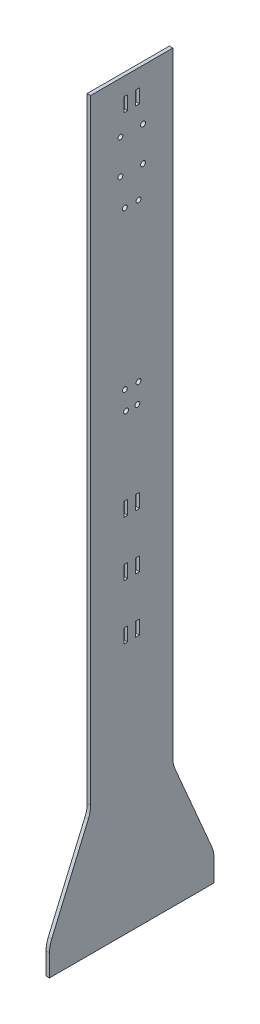
SolidWorks part; units mm, degrees
ref_plane "Front Plane" through (0, 0, 0) normal (0, 0, 1) x (1, 0, 0)
ref_plane "Top Plane" through (0, 0, 0) normal (0, 1, 0) x (1, 0, 0)
ref_plane "Right Plane" through (0, 0, 0) normal (1, 0, 0) x (0, 0, -1)
sketch "Sketch1" plane through (0, 0, 0) normal (1, 0, 0) x (0, 0, -1)
  line L1 (-38.1, 457.2) -> (38.1, 457.2)
  line L2 (-38.1, 457.2) -> (-38.1, -457.2)
  line L3 (-38.1, -457.2) -> (38.1, -457.2)
  line L4 (38.1, 457.2) -> (38.1, -457.2)
  line L5 (-38.1, 457.2) -> (38.1, -457.2) construction
  line L6 (-38.1, -457.2) -> (38.1, 457.2) construction
  point P0 (0, 0)
  dimension "D1" = 914.4
  dimension "D2" = 76.2
extrude "Boss-Extrude1" add sketch "Sketch1" along normal blind 3.175
sketch "Sketch2" plane through (3.175, 0, 0) normal (1, 0, 0) x (0, 0, -1)
  line L0 (-38.1, -457.2) -> (38.1, -457.2) construction
  line L1 (3.722, -204.5335) -> (7.278, -204.5335)
  line L2 (3.722, -204.5335) -> (3.722, -217.4875)
  line L3 (3.722, -217.4875) -> (7.278, -217.4875)
  line L4 (7.278, -204.5335) -> (7.278, -217.4875)
  line L5 (3.722, -204.5335) -> (7.278, -217.4875) construction
  line L6 (3.722, -217.4875) -> (7.278, -204.5335) construction
  point P0 (5.5, -211.0105)
  dimension "D1" = 3.556
  dimension "D2" = 12.954
  dimension "D3" = 239.7125
  dimension "D4" = 3.722
extrude "Cut-Extrude1" cut sketch "Sketch2" against normal through all
mirror "Mirror1" about plane through (0, 0, 0) normal (0, 0, 1) of "Cut-Extrude1"
pattern_linear "LPattern1" count 2 spacing 50.8 along (0, 1, 0) count 2 spacing 50.8 along (0, -1, 0) of "Mirror1", "Cut-Extrude1"
sketch "Sketch3" plane through (3.175, 0, 0) normal (1, 0, 0) x (0, 0, -1)
  line L0 (7.278, -153.7335) -> (3.722, -153.7335) construction
  line L1 (3.722, 170.9081) -> (7.278, 170.9081)
  line L2 (3.722, 170.9081) -> (3.722, 157.9541)
  line L3 (3.722, 157.9541) -> (7.278, 157.9541)
  line L4 (7.278, 170.9081) -> (7.278, 157.9541)
  line L5 (3.722, 170.9081) -> (7.278, 157.9541) construction
  line L6 (3.722, 157.9541) -> (7.278, 170.9081) construction
  line L7 (7.278, -166.6875) -> (7.278, -153.7335) construction
  line L9 (0, 0) -> (0, 53.0447) construction
  line L10 (-3.722, 157.9541) -> (-7.278, 170.9081) construction
  line L11 (-3.722, 170.9081) -> (-7.278, 157.9541) construction
  line L12 (-7.278, 170.9081) -> (-7.278, 157.9541)
  line L13 (-3.722, 157.9541) -> (-7.278, 157.9541)
  line L14 (-3.722, 170.9081) -> (-3.722, 157.9541)
  line L15 (-3.722, 170.9081) -> (-7.278, 170.9081)
  point P0 (5.5, 164.4311)
  point P19 (-5.5, 164.4311)
extrude "Cut-Extrude2" cut sketch "Sketch3" against normal through all
hole_wizard "#8 Clearance Hole1" positions "Sketch4" profile "Sketch5" hole size "#8" standard "ANSI Inch" end condition through all
sketch "Sketch4" plane through (3.175, 0, 0) normal (1, 0, 0) x (0, 0, -1)
  point P0 (6.35, -64.5237)
  point P3 (-6.35, -64.5237)
  point P6 (6.35, 81.272)
  point P9 (-6.35, 81.272)
  point P12 (5.25, -82.2261)
  point P15 (-5.25, -82.2261)
sketch "Sketch5" plane through (3.175, -64.5237, -6.35) normal (0, 1, 0) x (0, 0, -1)
  line L0 (0, 0) -> (0, 3.175)
  line L1 (0, 3.175) -> (2.2479, 3.175)
  line L2 (2.2479, 3.175) -> (2.2479, 0)
  line L5 (2.2479, 0) -> (0, 0)
  line L11 (0, -6.35) -> (0, 107.95) construction
  dimension "Thru Hole Dia." = 4.4958
  dimension "Thru Hole Depth" = 3.175
sketch "Sketch6" plane through (3.175, 0, 0) normal (1, 0, 0) x (0, 0, -1)
  line L0 (0, -457.2) -> (0, 187.325) construction
  line L1 (-38.1, -457.2) -> (38.1, -457.2) construction
  line L2 (-38.1, 187.325) -> (38.1, 187.325)
  line L4 (-38.1, 457.2) -> (-38.1, -457.2) construction
  line L5 (38.1, -457.2) -> (38.1, 457.2) construction
  dimension "D1" = 644.525
extrude "Cut-Extrude3" cut sketch "Sketch6" against normal through all and the other way through all
sketch "Sketch7" plane through (3.175, 0, 0) normal (1, 0, 0) x (0, 0, -1)
  line L0 (0, -457.2) -> (0, -501.65) construction
  line L1 (-38.1, -457.2) -> (38.1, -457.2) construction
  line L2 (-38.1, -457.2) -> (-38.1, -501.65)
  line L3 (-38.1, -501.65) -> (0, -501.65)
  line L4 (38.1, -457.2) -> (38.1, -501.65)
  line L5 (38.1, -501.65) -> (0, -501.65)
  line L6 (-38.1, -457.2) -> (38.1, -457.2)
  dimension "D1" = 44.45
extrude "Boss-Extrude2" add sketch "Sketch7" against normal up to surface (3.175 mm away) up to face at (0, -160.2105, 5.5)
sketch "Sketch8" plane through (3.175, 0, 0) normal (1, 0, 0) x (0, 0, -1)
  line L0 (-38.1, -387.35) -> (-76.2, -476.25)
  line L1 (-38.1, 187.325) -> (-38.1, -501.65) construction
  line L2 (-76.2, -476.25) -> (-76.2, -501.65)
  line L3 (-76.2, -501.65) -> (76.2, -501.65)
  line L4 (76.2, -501.65) -> (76.2, -476.25)
  line L5 (76.2, -476.25) -> (38.1, -387.35)
  line L6 (38.1, -501.65) -> (38.1, 187.325) construction
  line L7 (-38.1, -501.65) -> (38.1, -501.65) construction
  line L8 (-38.1, -387.35) -> (38.1, -387.35)
  dimension "D1" = 152.4
  dimension "D2" = 38.1
  dimension "D3" = 25.4
  dimension "D4" = 114.3
extrude "Boss-Extrude3" add sketch "Sketch8" against normal blind 3.175
fillet "Fillet1" radius 25.4 4 edges at (1.5875, -476.25, -76.2) (1.5875, -476.25, 76.2) (1.5875, -387.35, 38.1) (1.5875, -387.35, -38.1)
hole_wizard "#8 Clearance Hole2" positions "Sketch9" profile "Sketch10" hole size "#8" standard "ANSI Inch" end condition through all
sketch "Sketch9" plane through (0, 0, 0) normal (-1, 0, 0) x (0, 0, 1)
  point P0 (10.4775, 108.3263)
  point P3 (-10.4775, 108.3263)
  point P6 (-10.4775, 140.0763)
  point P13 (10.4775, 140.0763)
sketch "Sketch10" plane through (0, 108.3263, 10.4775) normal (0, 1, 0) x (0, 0, 1)
  line L0 (0, 0) -> (0, 3.175)
  line L1 (0, 3.175) -> (2.2479, 3.175)
  line L2 (2.2479, 3.175) -> (2.2479, 0)
  line L5 (2.2479, 0) -> (0, 0)
  line L11 (0, -6.35) -> (0, 107.95) construction
  dimension "Thru Hole Dia." = 4.4958
  dimension "Thru Hole Depth" = 3.175
